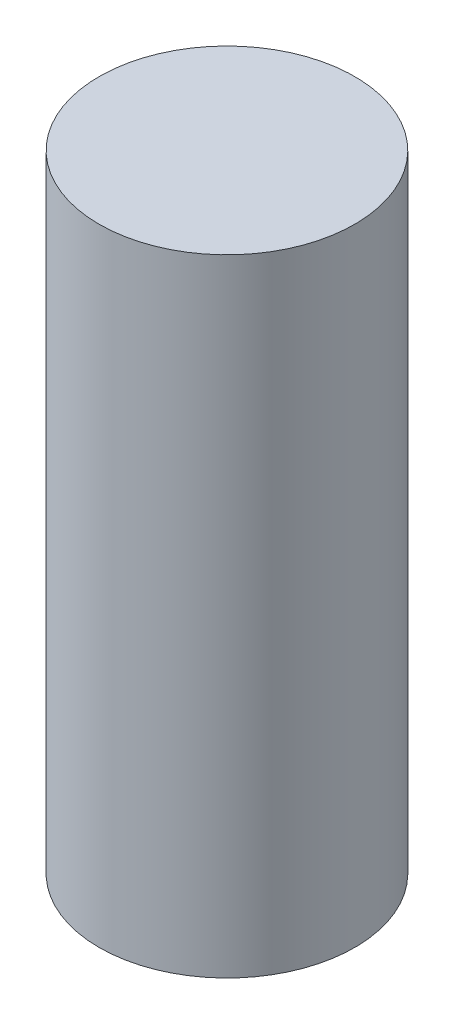
SolidWorks part; units mm, degrees
ref_plane "Front Plane" through (0, 0, 0) normal (0, 0, 1) x (1, 0, 0)
ref_plane "Top Plane" through (0, 0, 0) normal (0, 1, 0) x (1, 0, 0)
ref_plane "Right Plane" through (0, 0, 0) normal (1, 0, 0) x (0, 0, -1)
sketch "Sketch1" plane through (0, 0, 0) normal (0, 1, 0) x (1, 0, 0)
  circle A0 centre (0, 0) radius 2.45
  dimension "D1" = 4.9
extrude "Boss-Extrude1" add sketch "Sketch1" along normal blind 12
